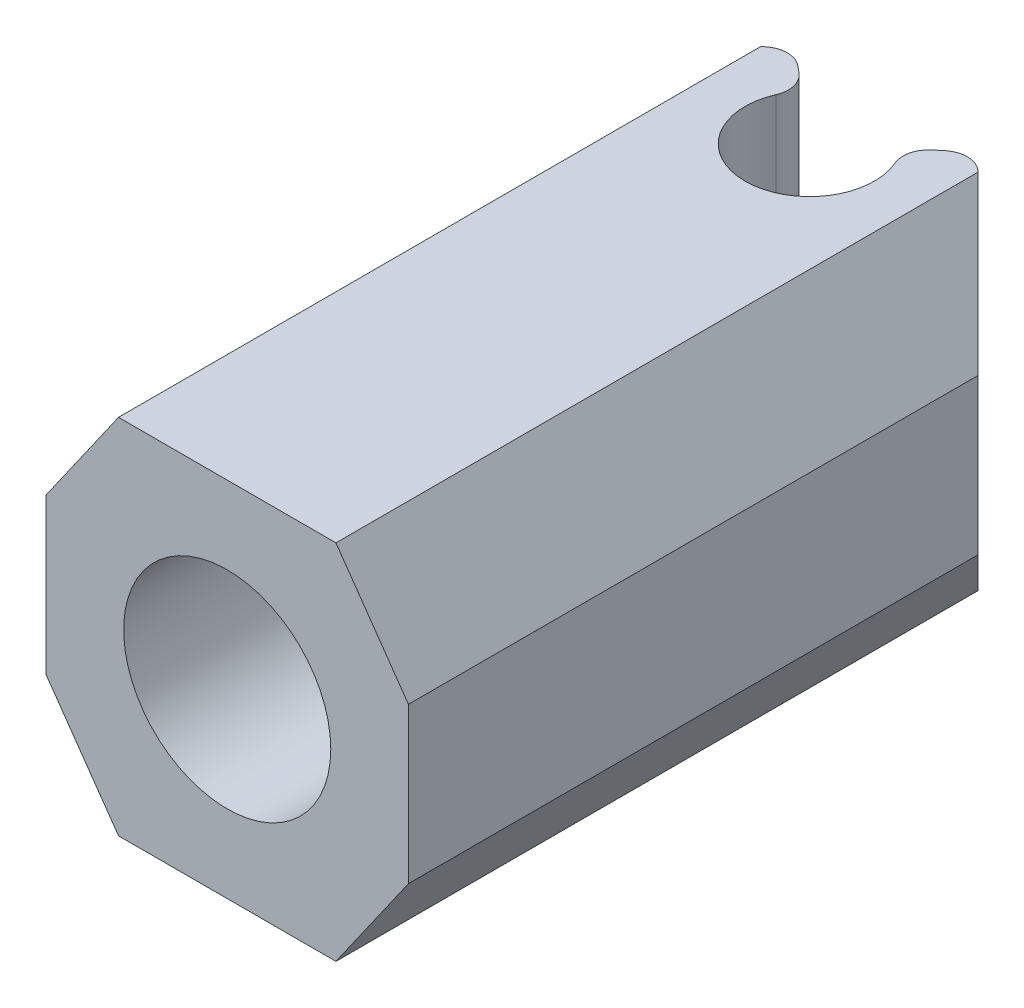
SolidWorks part; units mm, degrees
material "ABS"
ref_plane "Front Plane" through (0, 0, 0) normal (0, 0, 1) x (1, 0, 0)
ref_plane "Top Plane" through (0, 0, 0) normal (0, 1, 0) x (1, 0, 0)
ref_plane "Right Plane" through (0, 0, 0) normal (1, 0, 0) x (0, 0, -1)
sketch "Sketch1" plane through (0, 0, 0) normal (0, 1, 0) x (1, 0, 0)
  line L1 (7, 7.5) -> (-7, 7.5)
  line L2 (7, 7.5) -> (7, -7.5)
  line L3 (7, -7.5) -> (-7, -7.5)
  line L4 (-7, 7.5) -> (-7, -7.5)
  line L5 (7, 7.5) -> (-7, -7.5) construction
  line L6 (7, -7.5) -> (-7, 7.5) construction
  point P0 (0, 0)
  dimension "D1" = 15
  dimension "D2" = 14
extrude "Boss-Extrude1" add sketch "Sketch1" along normal mid plane 14
sketch "Sketch3" plane through (0, 0, 7.5) normal (0, 0, 1) x (1, 0, 0)
  circle A0 centre (0, 0) radius 4
  point P2 (0, 0)
  point P3 (0, 0)
  dimension "D1" = 8
extrude "Cut-Extrude1" cut sketch "Sketch3" against normal through all
sketch "Sketch4" plane through (0, 0, -7.5) normal (0, 0, -1) x (-1, 0, 0)
  line L2 (-7, -7) -> (7, -7)
  line L3 (-7, -7) -> (-7, 7)
  line L4 (-7, 7) -> (7, 7)
  line L5 (7, -7) -> (7, 7)
  line L6 (-7, -7) -> (7, 7) construction
  line L7 (-7, 7) -> (7, -7) construction
  point P0 (0, 0)
extrude "Boss-Extrude2" add sketch "Sketch4" along normal blind 12
sketch "Sketch7" plane through (0, 0, 0) normal (0, 1, 0) x (1, 0, 0)
  line L1 (-7, 19.5) -> (7, 19.5) construction
  circle A0 centre (0, 15) radius 6
  dimension "D1" = 12
  dimension "D2" = 4.5
extrude "Cut-Extrude7" cut sketch "Sketch7" against normal mid plane 6
sketch "Sketch8" plane through (0, -3, 0) normal (0, 1, 0) x (1, 0, 0)
  circle A0 centre (0, 15) radius 2.5
  arc A1 (-3.9686, 19.5) -> (3.9686, 19.5) centre (0, 15) ccw construction
  point P2 (0, 0)
  dimension "D1" = 5
extrude "Cut-Extrude8" cut sketch "Sketch8" against normal through all both and the other way through all
sketch "Sketch9" plane through (0, 0, 0) normal (1, 0, 0) x (0, 0, -1)
  line L0 (19.5, 7) -> (19.5, -7) construction
  line L1 (15, -3) -> (19.5, -3)
  line L2 (15, -3) -> (15, 3)
  line L3 (15, 3) -> (19.5, 3)
  line L4 (19.5, -3) -> (19.5, 3)
  line L5 (15, -3) -> (19.5, 3) construction
  line L6 (15, 3) -> (19.5, -3) construction
  point P0 (17.25, 0)
  point P5 (0, 0)
  dimension "D1" = 4.5
  dimension "D2" = 6
extrude "Cut-Extrude9" cut sketch "Sketch9" against normal through all both and the other way through all
sketch "Sketch12" plane through (0, 3, 0) normal (0, -1, 0) x (1, 0, 0)
  circle A0 centre (0, -15) radius 4 construction
chamfer "Chamfer1" distance 5 angle 45 2 edges at (7, -5, -19.5) (-7, -5, -19.5)
sketch "Sketch13" plane through (0, -3, 0) normal (0, 1, 0) x (1, 0, 0)
  circle A0 centre (0, 15) radius 3.5
  circle A1 centre (0, 15) radius 2.5 construction
  circle A2 centre (0, 15) radius 2.5
  dimension "D1" = 7
extrude "Boss-Extrude3" add sketch "Sketch13" along normal blind 1
sketch "Sketch14" plane through (0, 7, 0) normal (0, 1, 0) x (1, 0, 0)
  line L0 (0, 15) -> (11.2775, 24.463) construction
  line L1 (0, 15) -> (-11.7513, 24.8605) construction
  line L2 (0, 15) -> (0, 19.5) construction
  line L3 (-2, 19.5) -> (2, 19.5) construction
  line L4 (0, 15) -> (11.2775, 24.463)
  line L5 (11.2775, 24.463) -> (-11.7513, 24.8605)
  line L6 (-11.7513, 24.8605) -> (0, 15)
  dimension "D1" = 100
  dimension "D2" = 50
extrude "Cut-Extrude10" cut sketch "Sketch14" against normal blind 6
chamfer "Chamfer2" distance 4 angle 35 2 edges at (7, 7, -3.5) (-7, 7, -3.5)
chamfer "Chamfer3" distance 4 angle 35 2 edges at (-7, -7, -3.5) (7, -7, -3.5)
fillet "Fillet1" radius 1 4 edges at (-1.9151, 5, -16.607) (1.9151, 5, -16.607) (-3.5343, 5, -17.9657) (3.5343, 5, -17.9657)
fillet "Fillet2" radius 4 2 edges at (-2, -5, -19.5) (2, -5, -19.5)
sketch "Sketch15" plane through (0, 0, 0) normal (0, 1, 0) x (1, 0, 0)
  circle A0 centre (0, 15) radius 5.5 construction
  dimension "D1" = 11
